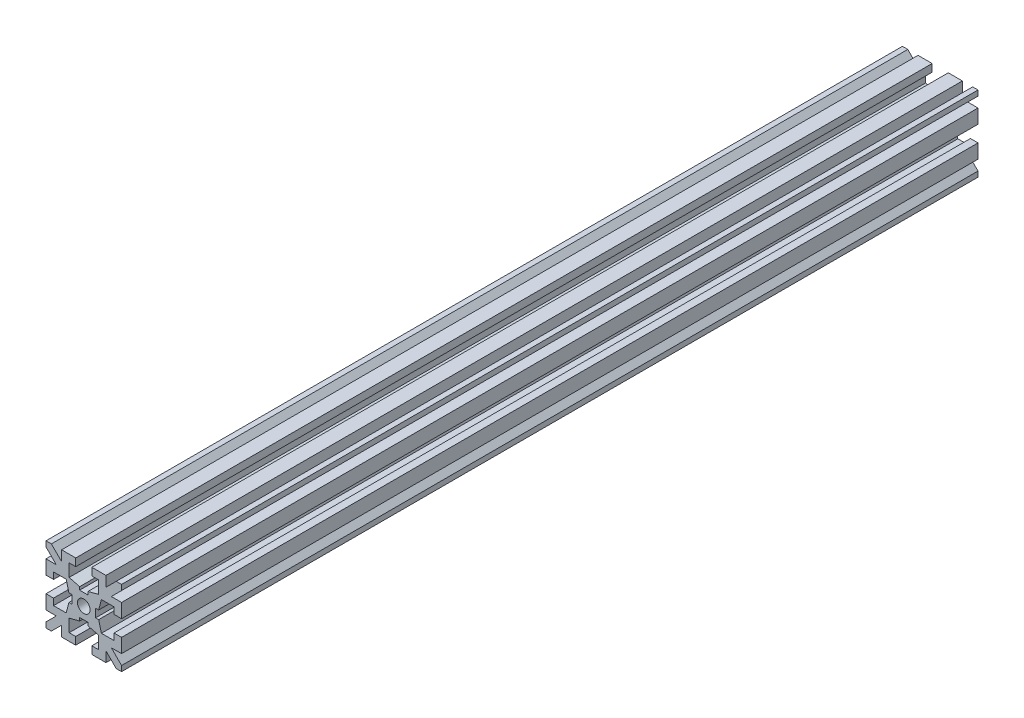
SolidWorks part; units mm, degrees
material "3.0205 (EN-AW 1200)"
ref_plane "Plano frontal" through (0, 0, 0) normal (0, 0, 1) x (1, 0, 0)
ref_plane "Plano superior" through (0, 0, 0) normal (0, 1, 0) x (1, 0, 0)
ref_plane "Plano direito" through (0, 0, 0) normal (1, 0, 0) x (0, 0, -1)
sketch "Esboço1" plane through (0, 0, 0) normal (0, 0, 1) x (1, 0, 0)
  line L0 (-25.7554, 0) -> (0, 0) construction
  line L1 (0, 0) -> (0, 21.5914) construction
  line L2 (0, 2.35) -> (-0.825, 2.35)
  line L3 (-0.825, 2.35) -> (-0.825, 2.95)
  line L4 (-0.825, 2.95) -> (-2.9, 3.5)
  line L5 (-2.9, 3.5) -> (-2.9, 6)
  line L6 (-2.9, 6) -> (-1.6, 6)
  line L7 (-1.6, 6) -> (-1.6, 7.5)
  line L8 (-1.6, 7.5) -> (-4.4, 7.5)
  line L9 (-4.4, 7.5) -> (-4.4, 5.4607)
  line L10 (-4.4, 5.4607) -> (-6.4393, 7.5)
  line L11 (-6.4393, 7.5) -> (-7.5, 7.5)
  line L12 (-7.5, 7.5) -> (0, 0) construction
  line L13 (-2.35, 0) -> (-2.35, 0.825)
  line L14 (-7.5, 6.4393) -> (-7.5, 7.5)
  line L15 (-5.4607, 4.4) -> (-7.5, 6.4393)
  line L16 (-7.5, 4.4) -> (-5.4607, 4.4)
  line L17 (-7.5, 1.6) -> (-7.5, 4.4)
  line L18 (-6, 1.6) -> (-7.5, 1.6)
  line L19 (-6, 2.9) -> (-6, 1.6)
  line L20 (-3.5, 2.9) -> (-6, 2.9)
  line L21 (-2.95, 0.825) -> (-3.5, 2.9)
  line L22 (-2.35, 0.825) -> (-2.95, 0.825)
  line L23 (-2.35, 0) -> (0, 0)
  line L24 (0, 0) -> (0, 2.35)
  dimension "D1" = 45
  dimension "D2" = 4.7
  dimension "D3" = 5.8
  dimension "D4" = 15
  dimension "D5" = 3.1
  dimension "D6" = 3.2
  dimension "D7" = 0.6
  dimension "D8" = 1.65
  dimension "D9" = 1.5
  dimension "D10" = 2.5
  dimension "D11" = 1.5
extrude "Ressalto-extrusão1" add sketch "Esboço1" along normal mid plane 170
mirror "Espelhar1" about plane through (0, 0, 0) normal (0, 1, 0) of "Ressalto-extrusão1"
mirror "Espelhar2" about plane through (0, 0, 0) normal (1, 0, 0) of "Espelhar1", "Ressalto-extrusão1"
sketch "Esboço2" plane through (0, 0, 85) normal (0, 0, 1) x (1, 0, 0)
  circle A0 centre (0, 0) radius 1.25
  dimension "D1" = 2.5
extrude "Corte-extrusão1" cut sketch "Esboço2" against normal through all both and the other way through all
